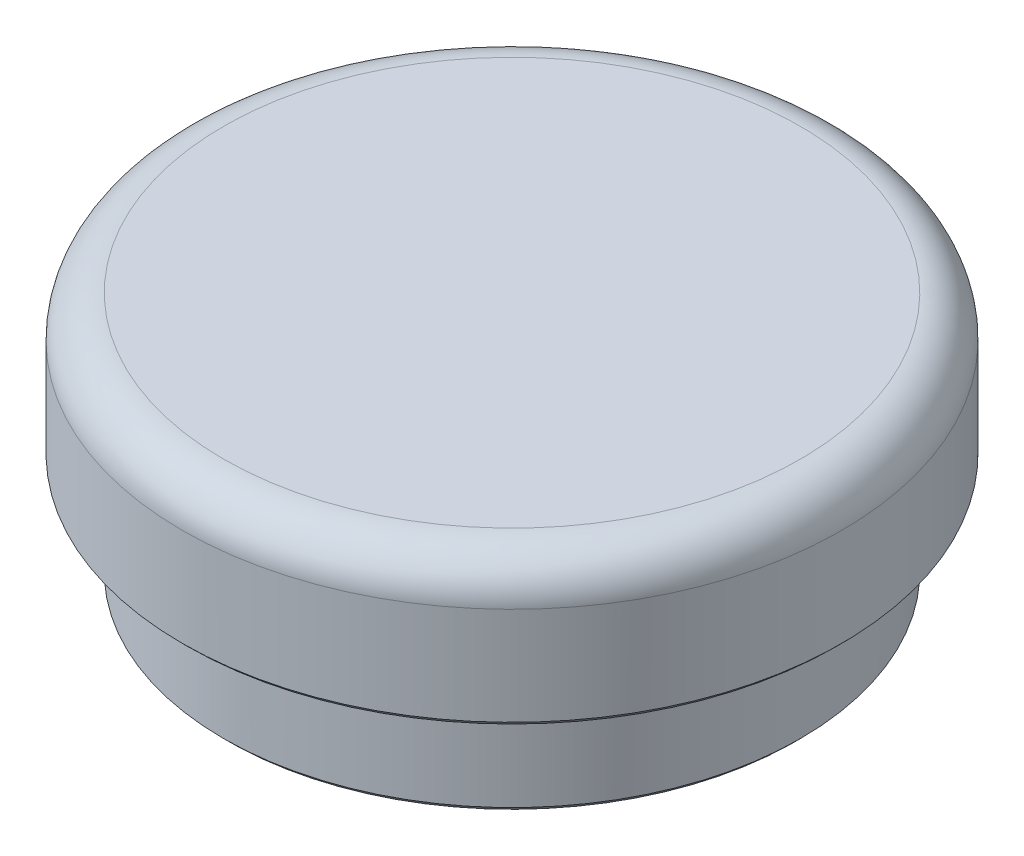
SolidWorks part; units mm, degrees
ref_plane "Front Plane" through (0, 0, 0) normal (0, 0, 1) x (1, 0, 0)
ref_plane "Top Plane" through (0, 0, 0) normal (0, 1, 0) x (1, 0, 0)
ref_plane "Right Plane" through (0, 0, 0) normal (1, 0, 0) x (0, 0, -1)
sketch "Sketch1" plane through (0, 0, 0) normal (0, 0, 1) x (1, 0, 0)
  line L0 (0, 0) -> (-14, 0)
  line L1 (-14, 0) -> (-14, 5)
  line L2 (-14, 5) -> (-16, 5)
  line L3 (-16, 5) -> (-16, 12)
  line L4 (-16, 12) -> (0, 12)
  line L5 (0, 12) -> (0, 0)
revolve "Revolve1" add sketch "Sketch1" angle 360 about L5
fillet "Fillet1" radius 2 1 edges at (0, 12, 16)
sketch "Sketch2" plane through (0, 0, 0) normal (0, -1, 0) x (1, 0, 0)
  circle A0 centre (0, 0) radius 10
extrude "Cut-Extrude1" cut sketch "Sketch2" against normal blind 9
chamfer "Chamfer1" distance 0.25 angle 45 2 edges at (0, 0, -10) (0, 0, 14)
chamfer "Chamfer2" distance 0.25 angle 45 1 edges at (0, 5, 16)
